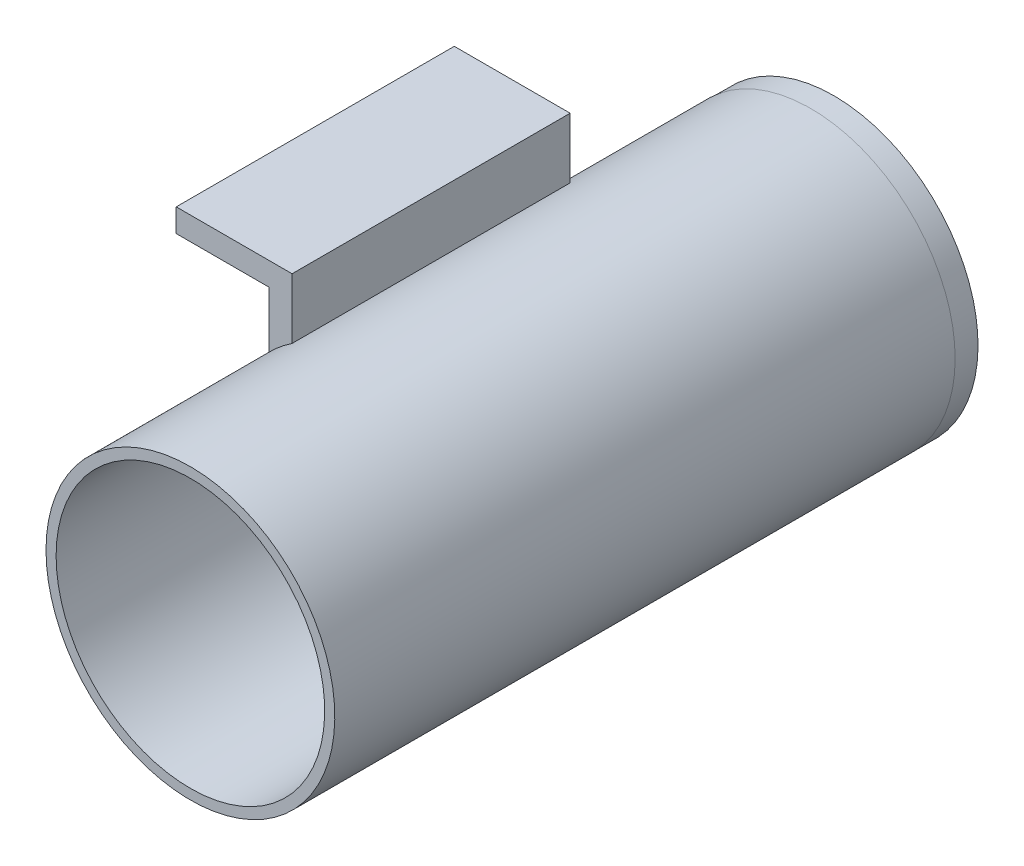
SolidWorks part; units mm, degrees
ref_plane "Front" through (0, 0, 0) normal (0, 0, 1) x (1, 0, 0)
ref_plane "Top" through (0, 0, 0) normal (0, 1, 0) x (1, 0, 0)
ref_plane "Right" through (0, 0, 0) normal (1, 0, 0) x (0, 0, -1)
sketch "Sketch1" plane through (0, 0, 0) normal (0, 0, 1) x (1, 0, 0)
  line L1 (-9.812, 11.8757) -> (-6.637, 11.8757)
  line L2 (-9.812, 11.8757) -> (-9.812, 0.8757)
  line L3 (-9.812, 0.8757) -> (-6.637, 0.8757)
  line L4 (-6.637, 11.8757) -> (-6.637, 0.8757)
  line L5 (-9.812, 8.7007) -> (-22.512, 8.7007)
  line L6 (-9.812, 8.7007) -> (-9.812, 11.8757)
  line L7 (-9.812, 11.8757) -> (-22.512, 11.8757)
  line L8 (-22.512, 8.7007) -> (-22.512, 11.8757)
  dimension "D1" = 11
  dimension "D2" = 3.175
  dimension "D3" = 3.175
  dimension "D4" = 12.7
extrude "Boss-Extrude1" add sketch "Sketch1" along normal blind 38.1 contours L8 L5 L2 L7 | L4 L1 L2 L3
sketch "Sketch2" plane through (0, 0, 0) normal (0, 0, -1) x (-1, 0, 0)
  circle A0 centre (-4.3298, -12.862) radius 19.7846
  circle A1 centre (-4.3298, -12.862) radius 18.4
extrude "Boss-Extrude2" add sketch "Sketch2" against normal blind 63 and the other way blind 22
sketch "Sketch3" plane through (0, 0, -22) normal (0, 0, -1) x (-1, 0, 0)
  circle A0 centre (-4.3256, -12.8973) radius 19.749
extrude "Boss-Extrude3" add sketch "Sketch3" along normal blind 3.175
sketch "Sketch4" plane through (0, 0, -25.175) normal (0, 0, -1) x (-1, 0, 0)
  line L1 (-12.779, -19.0774) -> (-10.2549, -19.0774)
  line L2 (-12.779, -19.0774) -> (-12.779, -29.8463)
  line L3 (-12.779, -29.8463) -> (-10.2549, -29.8463)
  line L4 (-10.2549, -19.0774) -> (-10.2549, -29.8463)
extrude "Cut-Extrude1" cut sketch "Sketch4" against normal blind 3.175
